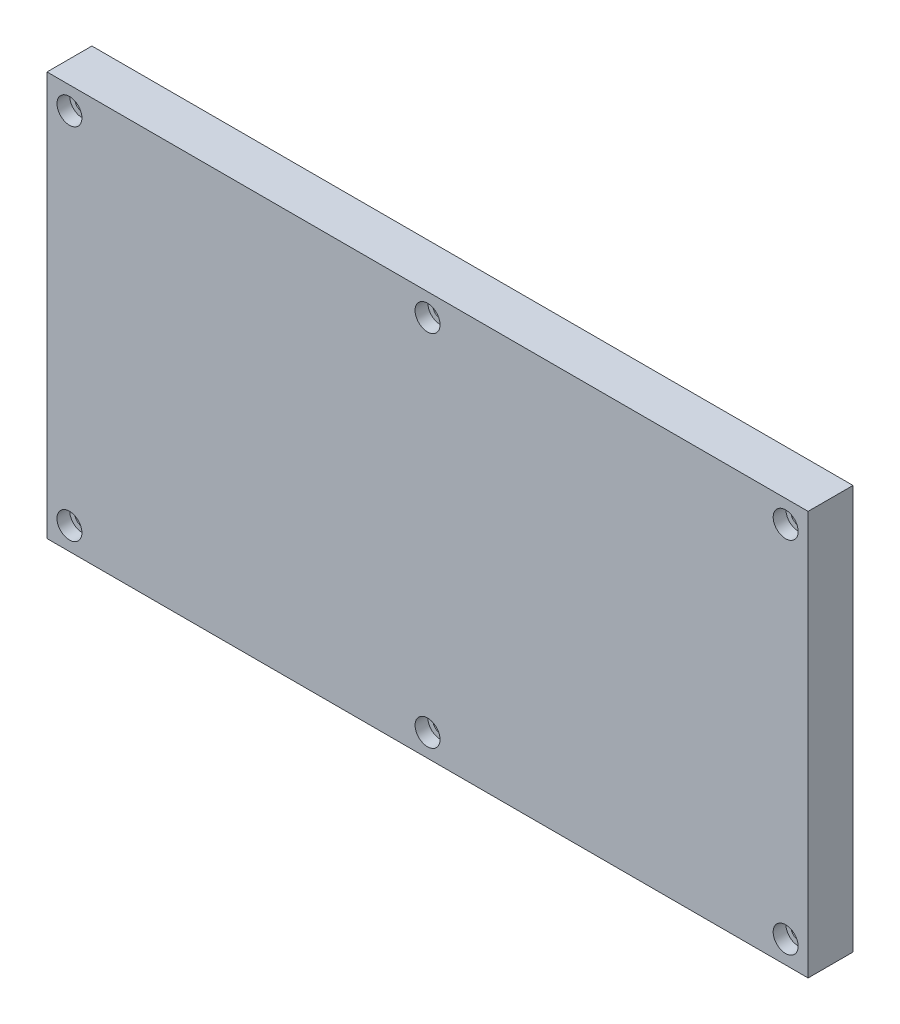
SolidWorks part; units mm, degrees
ref_plane "Front Plane" through (0, 0, 0) normal (0, 0, 1) x (1, 0, 0)
ref_plane "Top Plane" through (0, 0, 0) normal (0, 1, 0) x (1, 0, 0)
ref_plane "Right Plane" through (0, 0, 0) normal (1, 0, 0) x (0, 0, -1)
sketch "Sketch1" plane through (0, 0, 0) normal (0, 0, 1) x (1, 0, 0)
  line L1 (0, 0) -> (169.5, 0)
  line L2 (0, 0) -> (0, 90)
  line L3 (0, 90) -> (169.5, 90)
  line L4 (169.5, 0) -> (169.5, 90)
  dimension "D1" = 90
  dimension "D2" = 169.5
extrude "Boss-Extrude1" add sketch "Sketch1" along normal blind 10
sketch "Sketch2" plane through (0, 0, 10) normal (0, 0, 1) x (1, 0, 0)
  line L0 (0, 45) -> (169.5, 45) construction
  line L1 (0, 90) -> (0, 0) construction
  line L2 (169.5, 0) -> (169.5, 90) construction
  line L4 (169.5, 90) -> (0, 90) construction
  line L5 (84.75, 90) -> (84.75, 0) construction
  line L6 (0, 0) -> (169.5, 0) construction
hole_wizard "CBORE for #4 Socket Head Cap Screw1" positions "Sketch3" profile "Sketch4" counterbore size "#4" standard "ANSI Inch" end condition through all
sketch "Sketch3" plane through (0, 0, 10) normal (0, 0, 1) x (1, 0, 0)
  line L2 (0, 90) -> (0, 0) construction
  line L3 (169.5, 90) -> (0, 90) construction
  line L4 (0, 0) -> (169.5, 0) construction
  line L5 (169.5, 0) -> (169.5, 90) construction
  line L6 (84.75, 0) -> (84.75, 90) construction
  point P0 (5, 85)
  point P2 (164.5, 85)
  point P4 (164.5, 5)
  point P6 (5, 5)
  point P28 (84.75, 5)
  point P30 (84.75, 85)
  dimension "D1" = 5
  dimension "D2" = 5
  dimension "D3" = 5
  dimension "D4" = 5
  dimension "D5" = 5
  dimension "D6" = 5
  dimension "D7" = 5
  dimension "D8" = 5
  dimension "D9" = 5
  dimension "D10" = 5
sketch "Sketch4" plane through (5, 85, 10) normal (1, 0, 0) x (0, -1, 0)
  line L0 (0, 0) -> (0, 10)
  line L1 (0, 10) -> (1.6319, 10)
  line L3 (1.6319, 10) -> (1.632, 2.8448)
  line L4 (1.632, 2.8448) -> (2.7788, 2.8448)
  line L5 (2.7788, 2.8448) -> (2.7788, 0)
  line L7 (2.7788, 0) -> (0, 0)
  line L11 (0, -6.35) -> (0, 107.95) construction
  dimension "Thru Hole Dia." = 3.2639
  dimension "Thru Hole Depth" = 10
  dimension "C'Bore Dia." = 5.5575
  dimension "C'Bore Depth" = 2.8448
